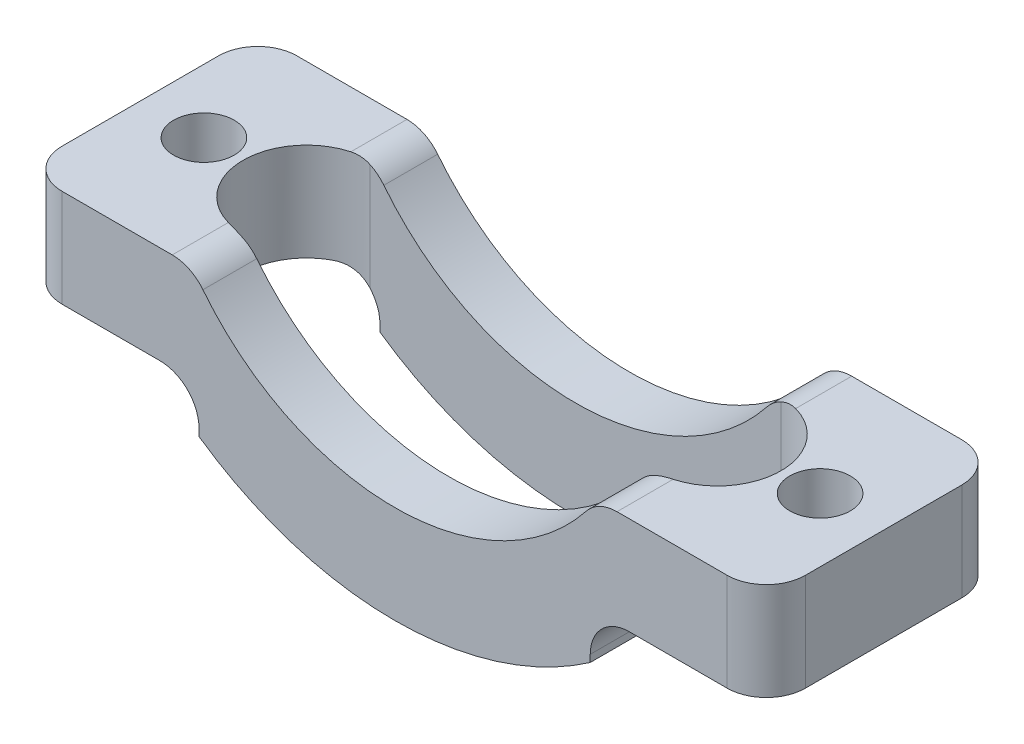
SolidWorks part; units mm, degrees
ref_plane "Front" through (0, 0, 0) normal (0, 0, 1) x (1, 0, 0)
ref_plane "Top" through (0, 0, 0) normal (0, 1, 0) x (1, 0, 0)
ref_plane "Right" through (0, 0, 0) normal (1, 0, 0) x (0, 0, -1)
sketch "Эскиз1" plane through (0, 0, 0) normal (0, 0, 1) x (1, 0, 0)
  line L0 (-19, -28) -> (-19, -33)
  line L3 (-19, -28) -> (-14, -28)
  line L4 (-14, -28) -> (-12.5, -21)
  line L5 (19, -28) -> (12.5, -28)
  line L6 (12.5, -28) -> (12.5, -21)
  line L7 (19, -28) -> (19, -33)
  line L8 (-19, -33) -> (-10, -33)
  line L9 (-10, -33) -> (-10, -35.3614)
  line L10 (19, -33) -> (10, -33)
  line L11 (10, -33) -> (10, -35.3614)
  line L12 (-14, -28) -> (14, -28)
  line L13 (14, -28) -> (14, -21) construction
  arc A1 (-12.5, -21) -> (12.5, -21) centre (0, -21) ccw
  arc A2 (-10, -35.3614) -> (10, -35.3614) centre (0, -21) ccw
  point P20 (0, -38.5)
  point P21 (10, -34.1807)
  dimension "D1" = 35
  dimension "D2" = 5
  dimension "D3" = 20
  dimension "D4" = 7
extrude "Бобышка-Вытянуть1" add sketch "Эскиз1" against normal blind 12 contours L9 A2 L11 L10 L7 L5 L12 A1 L3 L0 L8
fillet "Скругление2" radius 2 8 edges at (-19, -30.5, -12) (-19, -30.5, 0) (19, -30.5, -12) (19, -30.5, 0) (10.3562, -28, -6) (-10.3562, -28, -6) (-10, -33, -6) (10, -33, -6)
sketch "Эскиз2" plane through (0, -33, 0) normal (0, -1, 0) x (1, 0, 0)
  circle A0 centre (15.75, -6) radius 1.55
  circle A1 centre (-15.75, -6) radius 1.55
  dimension "D1" = 3.1
extrude "Вырез-Вытянуть3" cut sketch "Эскиз2" against normal blind 12
ref_plane "Плоскость1" through (0, -20.77, 0) normal (0, 1, 0) x (1, 0, 0)
sketch "Эскиз3" plane through (0, -20.77, 0) normal (0, 1, 0) x (1, 0, 0)
  line L0 (0, 0) -> (0, 12) construction
  line L1 (-10.5, 2.75) -> (10.5, 2.75)
  line L2 (-10.5, 9.25) -> (10.5, 9.25)
  line L3 (10, 12) -> (-10, 12) construction
  circle A0 centre (10.5, 6) radius 3.25
  circle A1 centre (-10.5, 6) radius 3.25
  point P2 (0, 12)
  point P12 (10, 5.5)
  point P13 (0, 0)
  point P16 (0, 0)
  point P17 (0, 6)
  dimension "D1" = 21
  dimension "D2" = 6.5
extrude "Вырез-Вытянуть4" cut sketch "Эскиз3" against normal through all contours A0 | L0 L1 A0 L2 | L1 L0 L2 A1 | A1 A0
